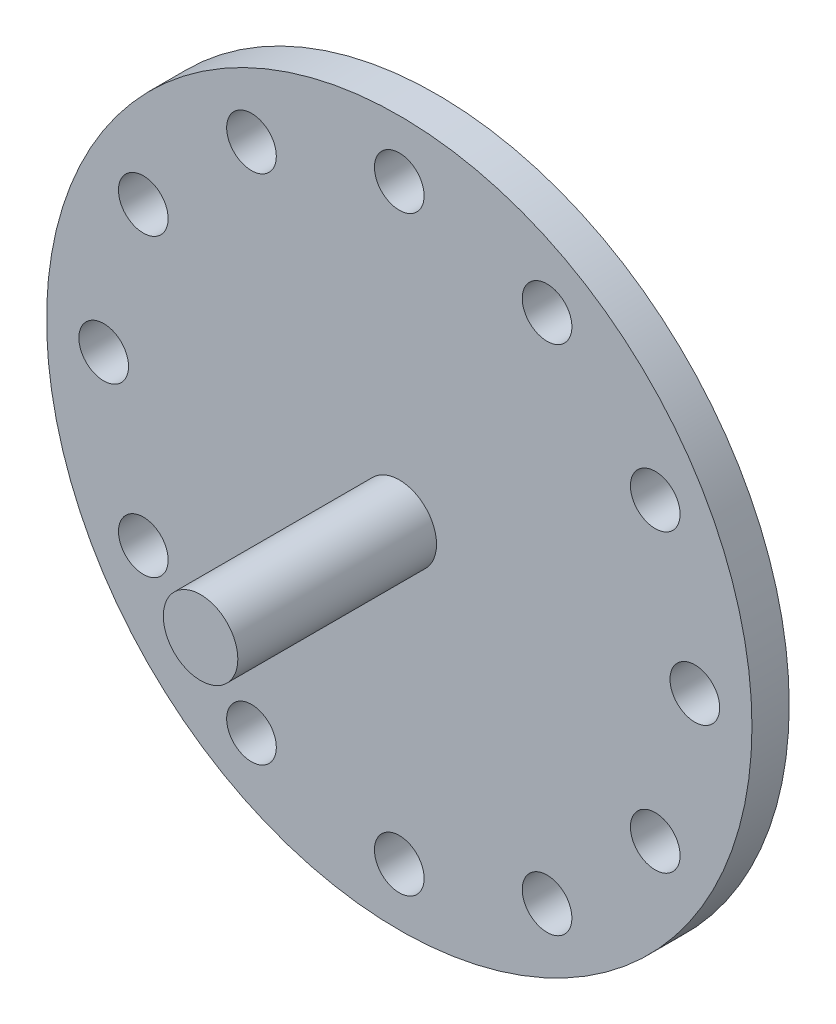
SolidWorks part; units mm, degrees
material "6061 Alloy"
ref_plane "Front Plane" through (0, 0, 0) normal (0, 0, 1) x (1, 0, 0)
ref_plane "Top Plane" through (0, 0, 0) normal (0, 1, 0) x (1, 0, 0)
ref_plane "Right Plane" through (0, 0, 0) normal (1, 0, 0) x (0, 0, -1)
sketch "Sketch1" plane through (0, 0, 0) normal (0, 0, 1) x (1, 0, 0)
  circle A0 centre (0, 0) radius 28.4
  circle A1 centre (23.8, 0) radius 2
  circle A2 centre (20.6114, -11.9) radius 2
  circle A3 centre (11.9, -20.6114) radius 2
  circle A4 centre (0, -23.8) radius 2
  circle A5 centre (-11.9, -20.6114) radius 2
  circle A6 centre (-20.6114, -11.9) radius 2
  circle A7 centre (-23.8, 0) radius 2
  circle A8 centre (-20.6114, 11.9) radius 2
  circle A9 centre (-11.9, 20.6114) radius 2
  circle A10 centre (0, 23.8) radius 2
  circle A11 centre (11.9, 20.6114) radius 2
  circle A12 centre (20.6114, 11.9) radius 2
  point P29 (0, 0)
  dimension "D1" = 56.8
  dimension "D2" = 4
  dimension "D3" = 23.8
  dimension "D4" = 12
extrude "Boss-Extrude1" add sketch "Sketch1" along normal blind 3
sketch "Sketch2" plane through (0, 0, 3) normal (0, 0, 1) x (1, 0, 0)
  circle A0 centre (0, 0) radius 3
  dimension "D1" = 6
extrude "Boss-Extrude2" add sketch "Sketch2" along normal blind 16
